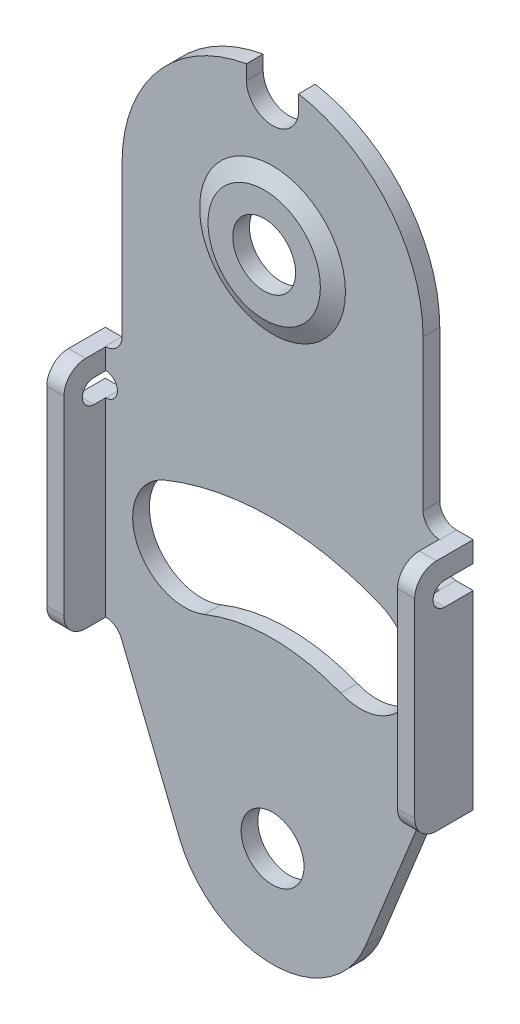
SolidWorks part; units mm, degrees
ref_plane "Front Plane" through (0, 0, 0) normal (0, 0, 1) x (1, 0, 0)
ref_plane "Top Plane" through (0, 0, 0) normal (0, 1, 0) x (1, 0, 0)
ref_plane "Right Plane" through (0, 0, 0) normal (1, 0, 0) x (0, 0, -1)
sketch "Sketch1" plane through (0, 0, 0) normal (0, 0, 1) x (1, 0, 0)
  line L0 (12.6669, 8.89) -> (13.97, 8.89)
  line L1 (7.0651, -2.8545) -> (11.4893, 8.0958)
  line L2 (-7.0651, -2.8545) -> (-11.4893, 8.0958)
  line L3 (-12.6669, 8.89) -> (-13.97, 8.89)
  line L4 (-13.97, 8.89) -> (-13.97, 26.67)
  line L5 (-13.97, 26.67) -> (-12.7, 26.67)
  line L6 (-11.43, 27.94) -> (-11.43, 39.37)
  line L7 (-1.9812, 49.53) -> (-1.9812, 50.627)
  line L8 (1.9812, 49.53) -> (1.9812, 50.627)
  line L9 (11.43, 27.94) -> (11.43, 39.37)
  line L10 (12.7, 26.67) -> (13.97, 26.67)
  line L11 (13.97, 26.67) -> (13.97, 8.89)
  line L12 (0, 0) -> (11.43, 27.94) construction
  line L13 (0, 0) -> (0, 39.37) construction
  line L14 (0, 0) -> (-11.43, 27.94) construction
  arc A0 (12.6669, 8.89) -> (11.4893, 8.0958) centre (12.6669, 7.62) ccw
  arc A1 (-7.0651, -2.8545) -> (7.0651, -2.8545) centre (0, 0) ccw
  arc A2 (-11.4893, 8.0958) -> (-12.6669, 8.89) centre (-12.6669, 7.62) ccw
  arc A3 (-12.7, 26.67) -> (-11.43, 27.94) centre (-12.7, 27.94) ccw
  arc A4 (-1.9812, 50.627) -> (-11.43, 39.37) centre (0, 39.37) ccw
  arc A5 (-1.9812, 49.53) -> (1.9812, 49.53) centre (0, 49.53) ccw
  arc A6 (11.43, 39.37) -> (1.9812, 50.627) centre (0, 39.37) ccw
  arc A7 (11.43, 27.94) -> (12.7, 26.67) centre (12.7, 27.94) ccw
  circle A8 centre (0, 0) radius 2.3876
  circle A9 centre (0, 39.37) radius 2.3876
  dimension "D1" = 7.62
  dimension "D9" = 1.27
  dimension "D10" = 11.43
  dimension "D15" = 4.7752
  dimension "D16" = 4.7752
  dimension "D2" = 8.89
  dimension "D3" = 27.94
  dimension "D4" = 3.9624
  dimension "D5" = 10.16
  dimension "D6" = 39.37
  dimension "D7" = 26.67
  dimension "D8" = 13.97
  dimension "D11" = 22.249
  dimension "D12" = 44
  dimension "D13" = 22
  dimension "D14" = 22.249
extrude "Extrude1" add sketch "Sketch1" along normal blind 1.27
sketch "Sketch2" plane through (0, 0, 1.27) normal (0, 0, 1) x (1, 0, 0)
  line L1 (-13.97, 26.67) -> (-12.6669, 26.67)
  line L2 (-13.97, 26.67) -> (-13.97, 8.89)
  line L3 (-13.97, 8.89) -> (-12.6669, 8.89)
  line L4 (-12.6669, 26.67) -> (-12.6669, 8.89)
  line L5 (12.6669, 8.89) -> (13.97, 8.89)
  line L6 (-13.97, 26.67) -> (-13.97, 8.89) construction
  line L7 (13.97, 8.89) -> (13.97, 26.67) construction
  line L8 (-13.97, 26.67) -> (-13.97, 8.89) construction
  line L9 (13.97, 8.89) -> (13.97, 26.67) construction
  line L10 (12.6669, 8.89) -> (12.6669, 26.67)
  line L11 (12.6669, 26.67) -> (13.97, 26.67)
  line L12 (13.97, 8.89) -> (13.97, 26.67)
extrude "Extrude2" add sketch "Sketch2" along normal blind 3.175
sketch "Sketch3" plane through (0, 0, 1.27) normal (0, 0, 1) x (1, 0, 0)
  arc A0 (-1.9812, 50.627) -> (-11.43, 39.37) centre (0, 39.37) ccw construction
  arc A1 (-1.9812, 50.627) -> (-11.43, 39.37) centre (0, 39.37) ccw construction
  circle A2 centre (0, 39.37) radius 5.5372
  circle A3 centre (0, 39.37) radius 2.3876 construction
  circle A4 centre (0, 39.37) radius 2.3876
  dimension "D1" = 11.0744
extrude "Extrude3" add sketch "Sketch3" along normal blind 0.635
sketch "Sketch4" plane through (0, 0, 0) normal (1, 0, 0) x (0, 0, -1)
  line L0 (-6.2866, 39.37) -> (3.8837, 39.37) construction
  line L1 (-1.905, 43.6372) -> (-1.27, 44.9072)
  line L2 (-1.905, 44.9072) -> (-1.905, 33.8328) construction
  line L3 (-1.27, 50.627) -> (-1.27, 39.37) construction
  line L4 (-1.27, 44.9072) -> (-1.905, 44.9072)
  line L5 (-1.905, 44.9072) -> (-1.905, 43.6372)
  line L6 (-0.635, 43.3324) -> (-0.635, 41.7576)
  line L8 (0, 39.37) -> (0, 50.627) construction
  line L9 (-0.635, 43.3324) -> (0, 44.5389)
  line L10 (0, 44.5389) -> (0, 43.3324)
  line L11 (-0.635, 41.7576) -> (0, 41.7576)
  line L12 (0, 41.7576) -> (0, 43.3324)
  dimension "D1" = 39.37
  dimension "D2" = 8.5344
  dimension "D3" = 11.0744
  dimension "D4" = 7.9248
  dimension "D5" = 10.3378
  dimension "D6" = 0.635
  dimension "D7" = 0.635
revolve "Cut-Revolve1" cut sketch "Sketch4" angle 360 about L0
sketch "Sketch5" plane through (0, 0, 1.27) normal (0, 0, 1) x (1, 0, 0)
  line L0 (0, 0) -> (-6.6605, 16.4853) construction
  line L1 (0, 0) -> (6.6605, 16.4853) construction
  line L2 (0, 0) -> (0, 39.0603) construction
  line L3 (12.6669, 26.67) -> (12.6669, 8.89) construction
  line L4 (-12.6669, 8.89) -> (-12.6669, 26.67) construction
  line L5 (12.6669, 26.67) -> (12.6669, 8.89) construction
  line L6 (-12.6669, 8.89) -> (-12.6669, 26.67) construction
  line L7 (-12.6669, 25.0952) -> (-12.6669, 23.3172)
  line L8 (12.6669, 25.0952) -> (12.6669, 23.3172)
  arc A0 (5.1762, 12.8115) -> (-5.1762, 12.8115) centre (0, 0) ccw
  arc A1 (5.1762, 12.8115) -> (8.1448, 20.1592) centre (6.6605, 16.4853) ccw
  arc A2 (8.1448, 20.1592) -> (-8.1448, 20.1592) centre (0, 0) ccw
  arc A3 (-8.1448, 20.1592) -> (-5.1762, 12.8115) centre (-6.6605, 16.4853) ccw
  arc A4 (-6.6605, 16.4853) -> (4.5383, 17.191) centre (0, 0) ccw construction
  arc A5 (-12.6669, 25.0952) -> (-12.6669, 23.3172) centre (-12.6669, 24.2062) cw
  circle A6 centre (0, 0) radius 2.3876 construction
  arc A7 (12.6669, 25.0952) -> (12.6669, 23.3172) centre (12.6669, 24.2062) ccw
  dimension "D2" = 21.7424
  dimension "D3" = 13.8176
  dimension "D5" = 17.78
  dimension "D6" = 0.889
  dimension "D7" = 24.2062
  dimension "D1" = 44
  dimension "D4" = 22
extrude "Cut-Extrude1" cut sketch "Sketch5" against normal through all
sketch "Sketch6" plane through (13.97, 0, 0) normal (1, 0, 0) x (0, 0, -1)
  line L0 (0, 25.0952) -> (-2.159, 25.0952)
  line L1 (0, 8.89) -> (0, 26.67) construction
  line L2 (-2.159, 23.3172) -> (0, 23.3172)
  line L3 (0, 23.3172) -> (0, 25.0952)
  line L4 (0, 25.0952) -> (-0.0039, 25.0952)
  arc A0 (-2.159, 25.0952) -> (-2.159, 23.3172) centre (-2.159, 24.2062) ccw
  dimension "D1" = 0.889
  dimension "D2" = 24.2062
  dimension "D3" = 2.159
extrude "Cut-Extrude2" cut sketch "Sketch6" against normal blind 1.3208 contours L0 A0 L2 L3
mirror "Mirror2" about plane through (0, 0, 0) normal (1, 0, 0) of "Cut-Extrude2"
sketch "Sketch7" plane through (0, 0, 0) normal (0, 0, -1) x (-1, 0, 0)
  text T0 "WWW.YORK-IND.COM" font "Century Gothic" height in points 4
extrude "Cut-Extrude3" cut sketch "Sketch7" against normal blind 0.0025
fillet "Fillet1" radius 1.651 4 edges at (13.3184, 8.89, 4.445) (13.3184, 26.67, 4.445) (-13.3184, 26.67, 4.445) (-13.3184, 8.89, 4.445)
